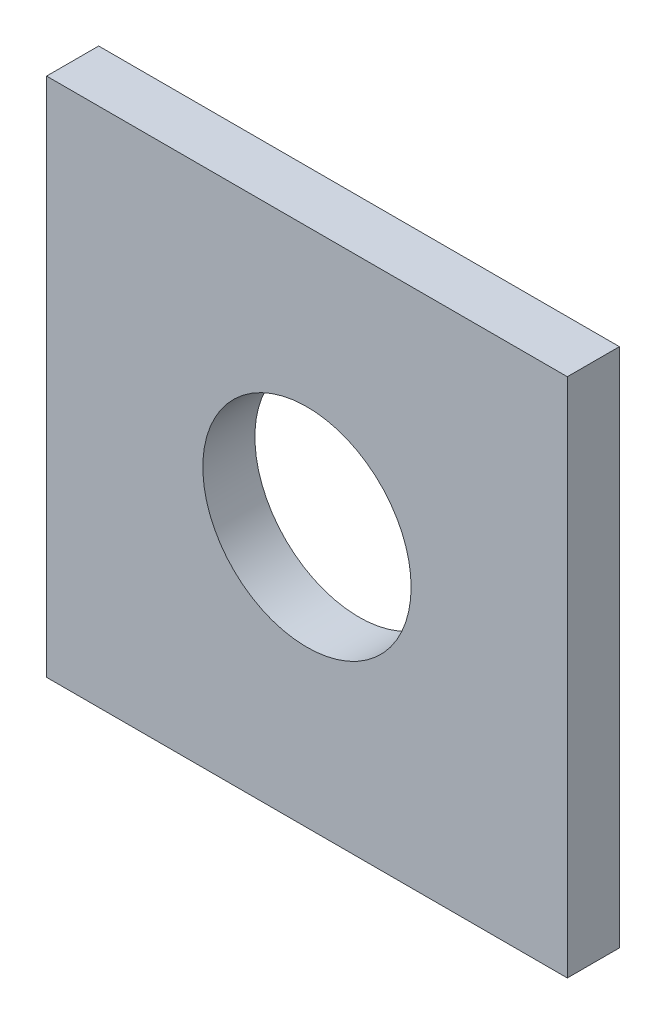
SolidWorks part; units mm, degrees
ref_plane "Plano frontal" through (0, 0, 0) normal (0, 0, 1) x (1, 0, 0)
ref_plane "Plano superior" through (0, 0, 0) normal (0, 1, 0) x (1, 0, 0)
ref_plane "Plano direito" through (0, 0, 0) normal (1, 0, 0) x (0, 0, -1)
sketch "Esboço1" plane through (0, 0, 0) normal (0, 0, 1) x (1, 0, 0)
  line L0 (0, 0) -> (0, 10)
  line L1 (0, 10) -> (10, 10)
  line L2 (10, 10) -> (10, 0)
  line L3 (10, 0) -> (0, 0)
  circle A0 centre (5, 5) radius 2
extrude "Ressalto-extrusão1" add sketch "Esboço1" along normal blind 1
